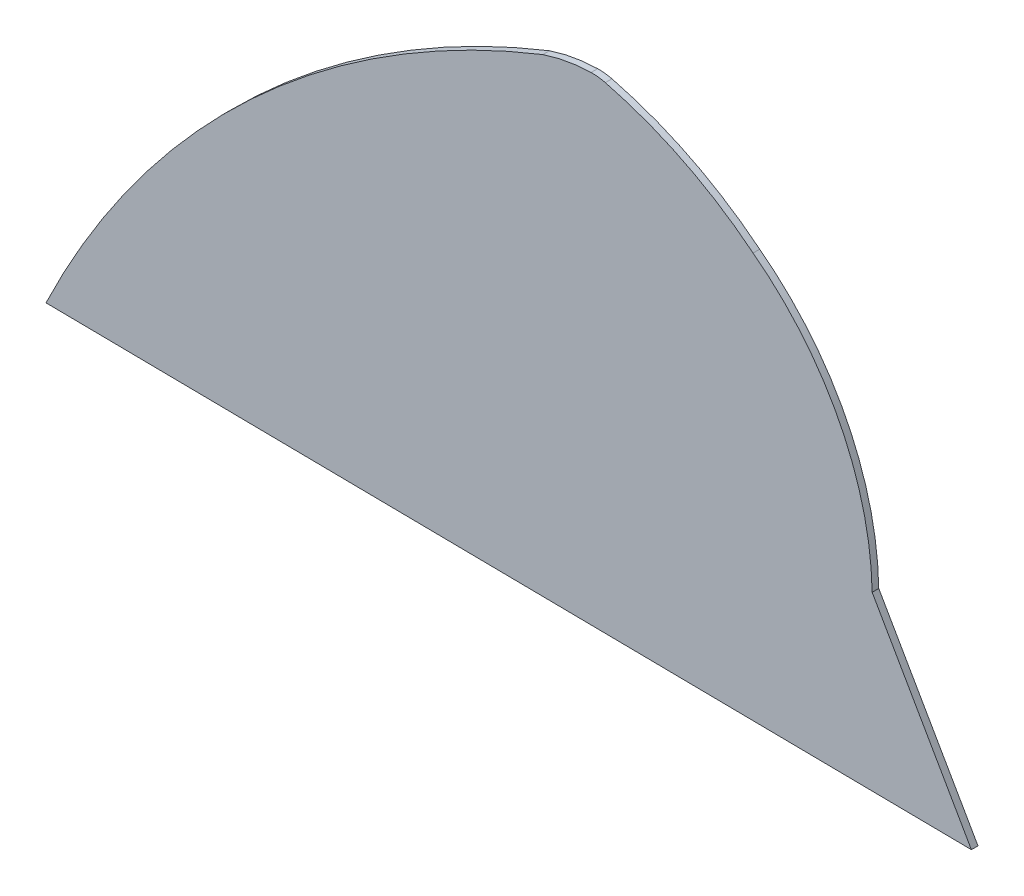
SolidWorks part; units mm, degrees
ref_plane "Ön Düzlem" through (0, 0, 0) normal (0, 0, 1) x (1, 0, 0)
ref_plane "Üst Düzlem" through (0, 0, 0) normal (0, 1, 0) x (1, 0, 0)
ref_plane "Sağ Düzlem" through (0, 0, 0) normal (1, 0, 0) x (0, 0, -1)
sketch "Çizim1" plane through (0, 0, 0) normal (0, 0, 1) x (1, 0, 0)
  line L0 (11.726, -2.7401) -> (15.8565, 682.2599) construction
  line L1 (-740.853, 6.1312) -> (664.147, -10.4307)
  line L2 (499.1778, 245.9513) -> (664.147, -10.4307) construction
  line L3 (100.3704, 687.6958) -> (92.2204, -3.6889) construction
  line L4 (664.147, -10.4307) -> (514.0043, 251.779)
  arc A0 (-740.853, 6.1312) -> (15.8565, 682.2599) centre (507.8481, -629.8783) cw construction
  arc A1 (15.8565, 682.2599) -> (100.3704, 687.6958) centre (79.9272, 345.8305) cw construction
  arc A2 (100.3704, 687.6958) -> (319.365, 585.8695) centre (-36.9515, 105.9565) cw construction
  arc A3 (319.365, 585.8695) -> (499.1778, 245.9513) centre (85.3083, 244.5376) cw construction
  arc A5 (15.9002, 707.2601) -> (88.7539, 720.1524) centre (94.7552, 473.948) cw
  arc A7 (333.8923, 606.2206) -> (514.0043, 251.779) centre (60.486, 244.3039) cw
  arc A8 (110.3487, 717.7265) -> (333.8923, 606.2206) centre (-33.6901, 149.1325) cw
  arc A9 (88.7539, 720.1524) -> (110.3487, 717.7265) centre (90.7033, 640.1761) cw
  arc A10 (-735.853, 6.0723) -> (15.9002, 707.2601) centre (535.9886, -603.9104) cw
  point P4 (15.9002, 707.2601)
  point P21 (-735.853, 6.0723)
  dimension "D8" = 80
  dimension "D1" = 685
  dimension "D2" = 1405
  dimension "D3" = 710
  dimension "D4" = 691.4328
  dimension "D5" = 25.0002
  dimension "D6" = 752.5789
  dimension "D7" = 833.0734
  dimension "D9" = 1400
  dimension "D10" = 723.7502
extrude "Yükseklik-Ekstrüzyon1" add sketch "Çizim1" along normal blind 10 contours A10 L1 L4 A7 A8 A9 A5
sketch "Çizim2" plane through (0, 0, 10) normal (0, 0, 1) x (1, 0, 0)
  line L0 (-735.853, 6.0723) -> (15.9002, 707.2601) construction
  line L1 (-11.8777, 695.8982) -> (65.8034, 511.6005)
  line L2 (-11.8777, 695.8982) -> (-49.9716, 679.8417) construction
  line L3 (-735.853, 6.0723) -> (-511.1902, 3.424)
  arc A0 (15.9002, 707.2601) -> (-735.853, 6.0723) centre (535.9886, -603.9104) ccw construction
  arc A1 (15.9002, 707.2601) -> (-735.853, 6.0723) centre (535.9886, -603.9104) ccw
  arc A2 (65.8034, 511.6005) -> (-511.1902, 3.424) centre (535.9886, -603.9104) ccw
  arc A3 (89.6427, 521.3513) -> (-555.5206, -80.4162) centre (535.9886, -603.9104) ccw construction
  point P6 (-11.8777, 695.8982)
  dimension "D4" = 90
  dimension "D2" = 1028.0064
  dimension "D3" = 1000
  dimension "D1" = 200
